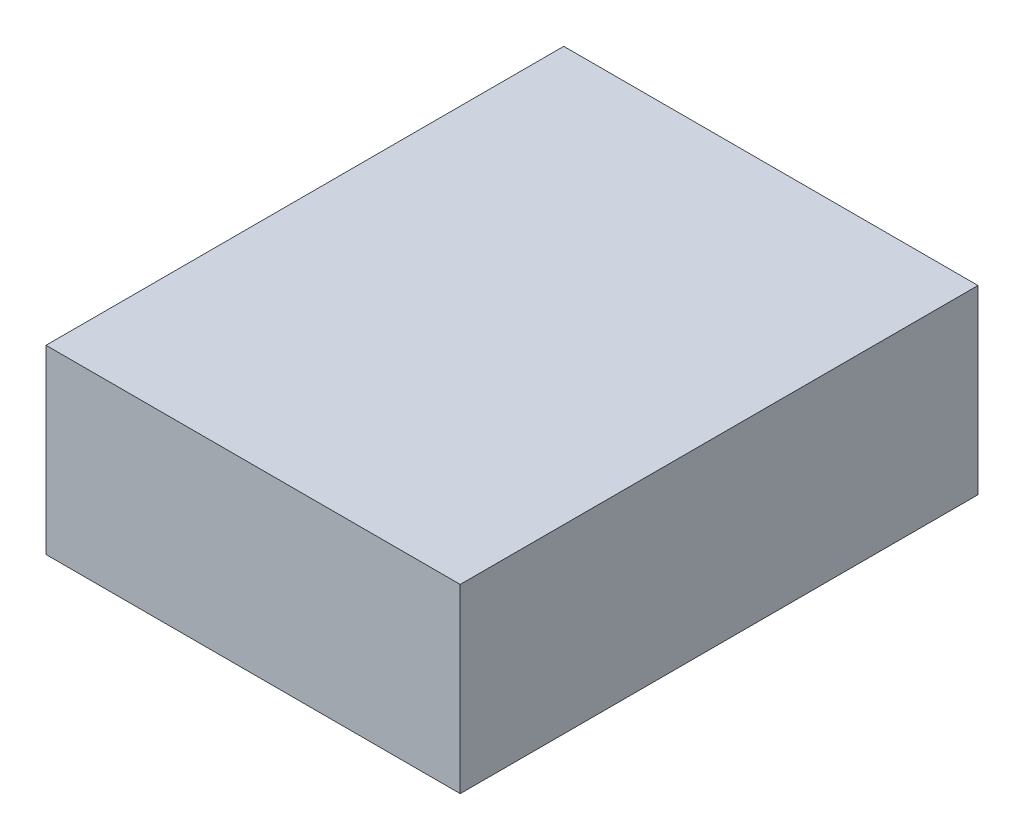
SolidWorks part; units mm, degrees
ref_plane "Ebene vorne" through (0, 0, 0) normal (0, 0, 1) x (1, 0, 0)
ref_plane "Ebene oben" through (0, 0, 0) normal (0, 1, 0) x (1, 0, 0)
ref_plane "Ebene rechts" through (0, 0, 0) normal (1, 0, 0) x (0, 0, -1)
sketch "Skizze1" plane through (0, 0, 0) normal (0, 1, 0) x (1, 0, 0)
  line L1 (-40, 50) -> (40, 50)
  line L2 (-40, 50) -> (-40, -50)
  line L3 (-40, -50) -> (40, -50)
  line L4 (40, 50) -> (40, -50)
  dimension "D1" = 100
  dimension "D2" = 80
  dimension "D3" = 50
  dimension "D4" = 40
extrude "Aufsatz-Linear austragen1" add sketch "Skizze1" along normal blind 35
